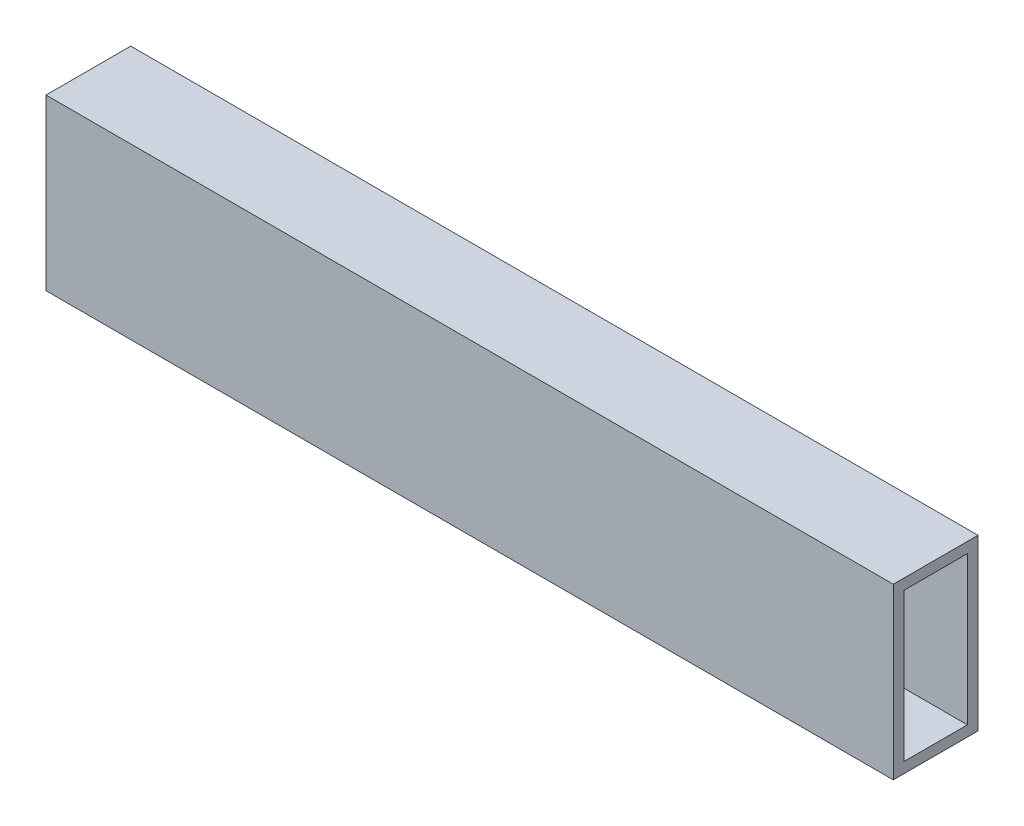
SolidWorks part; units mm, degrees
material "6061 Alloy"
ref_plane "Front Plane" through (0, 0, 0) normal (0, 0, 1) x (1, 0, 0)
ref_plane "Top Plane" through (0, 0, 0) normal (0, 1, 0) x (1, 0, 0)
ref_plane "Right Plane" through (0, 0, 0) normal (1, 0, 0) x (0, 0, -1)
sketch "Sketch1" plane through (0, 0, 0) normal (0, 1, 0) x (1, 0, 0)
  line L1 (-127, 12.7) -> (127, 12.7)
  line L2 (-127, 12.7) -> (-127, -12.7)
  line L3 (-127, -12.7) -> (127, -12.7)
  line L4 (127, 12.7) -> (127, -12.7)
  line L5 (-127, 12.7) -> (127, -12.7) construction
  line L6 (-127, -12.7) -> (127, 12.7) construction
  point P0 (0, 0)
  dimension "D1" = 254
  dimension "D2" = 25.4
extrude "Boss-Extrude1" add sketch "Sketch1" along normal mid plane 50.8
shell "Shell1" thickness 3.175
sketch "Sketch2" plane through (0, 25.4, 0) normal (0, 1, 0) x (1, 0, 0)
  line L0 (127, -12.7) -> (127, 12.7) construction
  circle A0 centre (114.3, 0) radius 3.175
  circle A1 centre (88.9, 0) radius 3.175
  circle A2 centre (63.5, 0) radius 3.175
  circle A3 centre (38.1, 0) radius 3.175
  circle A4 centre (12.7, 0) radius 3.175
  circle A5 centre (-12.7, 0) radius 3.175
  circle A6 centre (-38.1, 0) radius 3.175
  circle A7 centre (-63.5, 0) radius 3.175
  circle A8 centre (-88.9, 0) radius 3.175
  circle A9 centre (-114.3, 0) radius 3.175
  circle A10 centre (-139.7, 0) radius 3.175
  circle A11 centre (-165.1, 0) radius 3.175
  circle A12 centre (-190.5, 0) radius 3.175
  circle A13 centre (-215.9, 0) radius 3.175
  circle A14 centre (-241.3, 0) radius 3.175
  circle A15 centre (-266.7, 0) radius 3.175
  circle A16 centre (-292.1, 0) radius 3.175
  circle A17 centre (-317.5, 0) radius 3.175
  circle A18 centre (-342.9, 0) radius 3.175
  circle A19 centre (-368.3, 0) radius 3.175
  circle A20 centre (-393.7, 0) radius 3.175
  circle A21 centre (-419.1, 0) radius 3.175
  circle A22 centre (-444.5, 0) radius 3.175
  circle A23 centre (-469.9, 0) radius 3.175
  circle A24 centre (-495.3, 0) radius 3.175
  circle A25 centre (-520.7, 0) radius 3.175
  circle A26 centre (-546.1, 0) radius 3.175
  circle A27 centre (-571.5, 0) radius 3.175
  circle A28 centre (-596.9, 0) radius 3.175
  circle A29 centre (-622.3, 0) radius 3.175
  circle A30 centre (-647.7, 0) radius 3.175
  circle A31 centre (-673.1, 0) radius 3.175
  circle A32 centre (-698.5, 0) radius 3.175
  circle A33 centre (-723.9, 0) radius 3.175
  circle A34 centre (-749.3, 0) radius 3.175
  circle A35 centre (-774.7, 0) radius 3.175
  circle A36 centre (-800.1, 0) radius 3.175
  circle A37 centre (-825.5, 0) radius 3.175
  circle A38 centre (-850.9, 0) radius 3.175
  circle A39 centre (-876.3, 0) radius 3.175
  circle A40 centre (-901.7, 0) radius 3.175
  circle A41 centre (-927.1, 0) radius 3.175
  circle A42 centre (-952.5, 0) radius 3.175
  circle A43 centre (-977.9, 0) radius 3.175
  circle A44 centre (-1003.3, 0) radius 3.175
  circle A45 centre (-1028.7, 0) radius 3.175
  circle A46 centre (-1054.1, 0) radius 3.175
  circle A47 centre (-1079.5, 0) radius 3.175
  circle A48 centre (-1104.9, 0) radius 3.175
  circle A49 centre (-1130.3, 0) radius 3.175
  circle A50 centre (-1155.7, 0) radius 3.175
  circle A51 centre (-1181.1, 0) radius 3.175
  circle A52 centre (-1206.5, 0) radius 3.175
  circle A53 centre (-1231.9, 0) radius 3.175
  circle A54 centre (-1257.3, 0) radius 3.175
  circle A55 centre (-1282.7, 0) radius 3.175
  circle A56 centre (-1308.1, 0) radius 3.175
  circle A57 centre (-1333.5, 0) radius 3.175
  circle A58 centre (-1358.9, 0) radius 3.175
  circle A59 centre (-1384.3, 0) radius 3.175
  dimension "D2" = 6.35
  dimension "D1" = 12.7
  dimension "D4" = 25.4
  dimension "D3" = 60
extrude "Cut-Extrude1" [suppressed] cut sketch "Sketch2" against normal through all
equation "\"A\"= 1"
equation "\"B\"= 2"
equation "\"C\"= 1 / 8"
equation "\"D\"= 10"
equation "\"D1@Sketch1\"=\"D\""
equation "\"D2@Sketch1\"=\"A\""
equation "\"D1@Boss-Extrude1\"=\"B\""
equation "\"D1@Shell1\"=\"C\""
